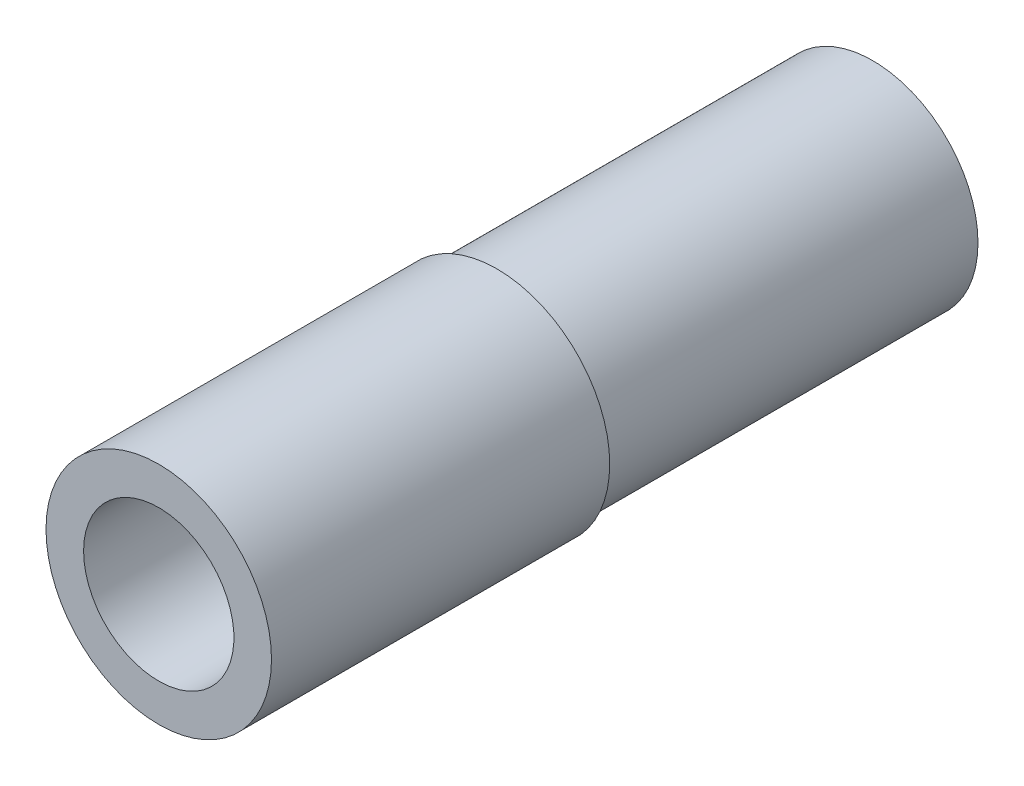
SolidWorks part; units mm, degrees
ref_plane "Front Plane" through (0, 0, 0) normal (0, 0, 1) x (1, 0, 0)
ref_plane "Top Plane" through (0, 0, 0) normal (0, 1, 0) x (1, 0, 0)
ref_plane "Right Plane" through (0, 0, 0) normal (1, 0, 0) x (0, 0, -1)
sketch "Sketch1" plane through (0, 0, 0) normal (0, 0, 1) x (1, 0, 0)
  circle A0 centre (0, 0) radius 15
  circle A1 centre (0, 0) radius 5
  dimension "D1" = 30
  dimension "D2" = 10
extrude "Boss-Extrude1" add sketch "Sketch1" along normal blind 45 contours A0
sketch "Sketch2" plane through (0, 0, 0) normal (0, 0, -1) x (-1, 0, 0)
  circle A0 centre (0, 0) radius 10
  dimension "D1" = 20
extrude "Cut-Extrude1" cut sketch "Sketch2" against normal through all
sketch "Sketch3" plane through (0, 0, 0) normal (0, 0, -1) x (-1, 0, 0)
  circle A0 centre (0, 0) radius 14
  dimension "D1" = 28
extrude "Boss-Extrude2" add sketch "Sketch3" along normal blind 50
sketch "Sketch5" plane through (0, 0, -50) normal (0, 0, -1) x (-1, 0, 0)
  circle A0 centre (0, 0) radius 10
  dimension "D1" = 20
extrude "Cut-Extrude2" cut sketch "Sketch5" against normal blind 18 contours A0
